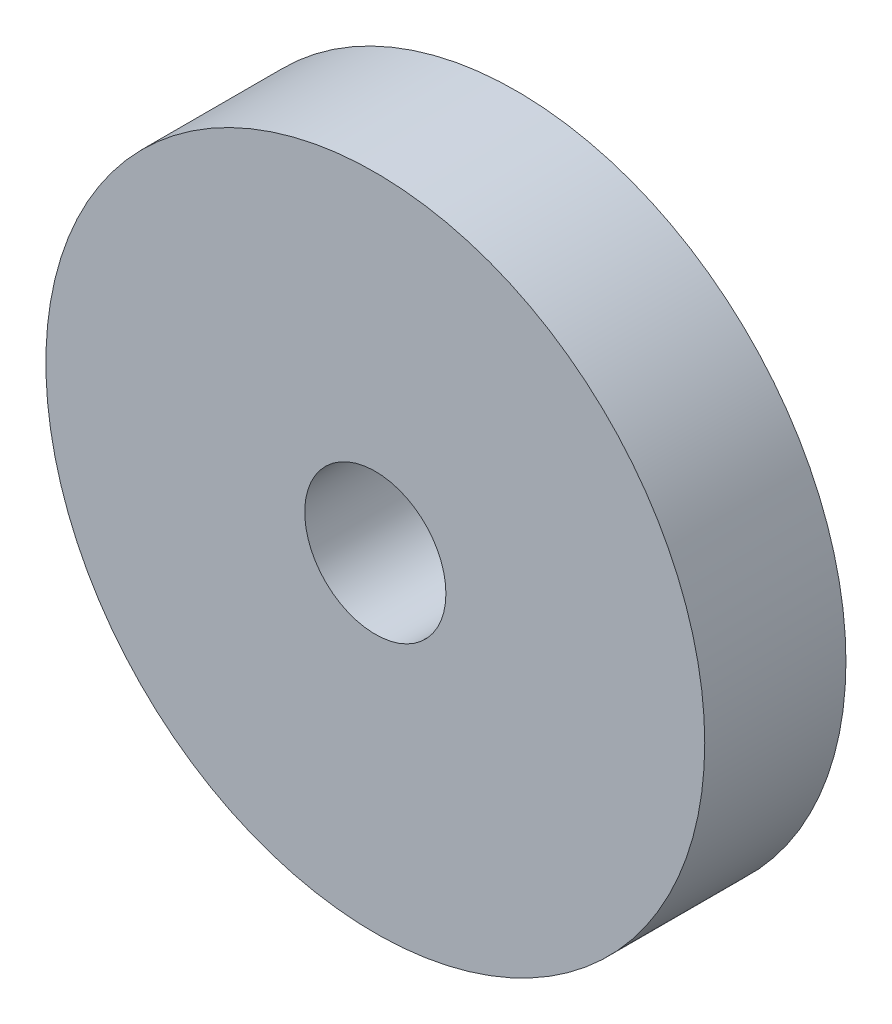
SolidWorks part; units mm, degrees
ref_plane "Front Plane" through (0, 0, 0) normal (0, 0, 1) x (1, 0, 0)
ref_plane "Top Plane" through (0, 0, 0) normal (0, 1, 0) x (1, 0, 0)
ref_plane "Right Plane" through (0, 0, 0) normal (1, 0, 0) x (0, 0, -1)
sketch "Sketch1" plane through (0, 0, 0) normal (0, 0, 1) x (1, 0, 0)
  circle A1 centre (0, 0) radius 7
extrude "Boss-Extrude1" add sketch "Sketch1" along normal blind 3
sketch "Sketch2" plane through (0, 0, 3) normal (0, 0, 1) x (1, 0, 0)
  circle A0 centre (0, 0) radius 1.5
extrude "Cut-Extrude1" cut sketch "Sketch2" against normal up to surface (3 mm away) up to face at (7, 0, 0)
